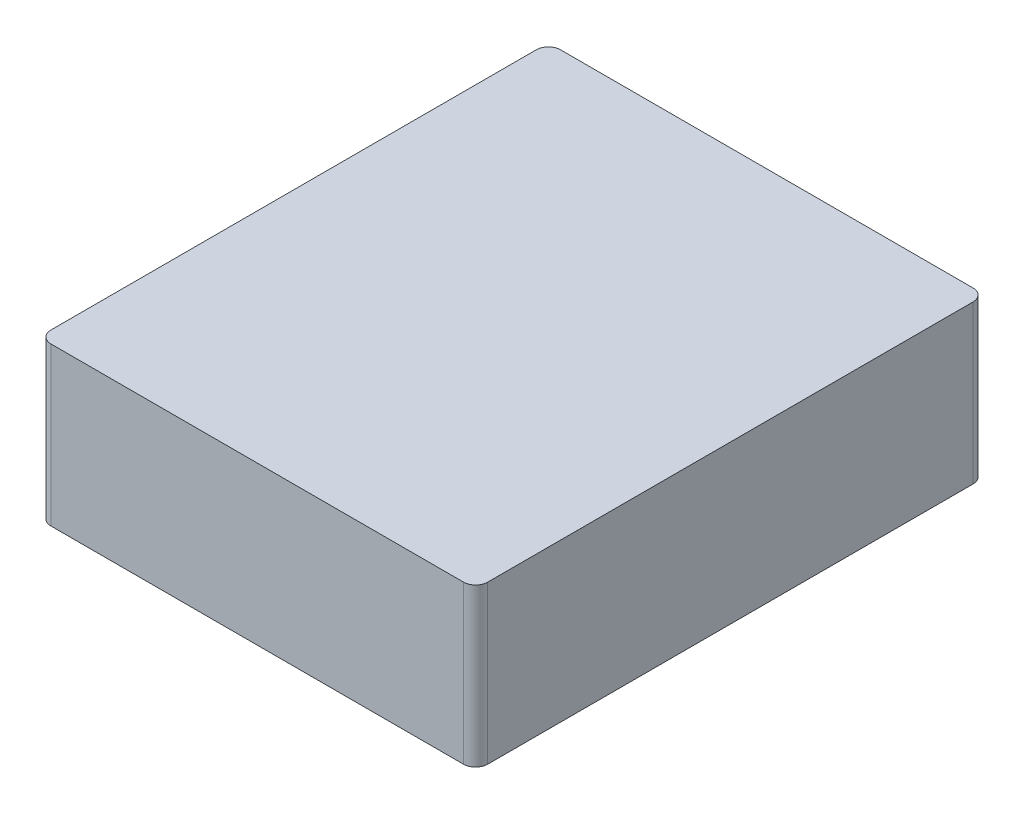
SolidWorks part; units mm, degrees
ref_plane "Front" through (0, 0, 0) normal (0, 0, 1) x (1, 0, 0)
ref_plane "Top" through (0, 0, 0) normal (0, 1, 0) x (1, 0, 0)
ref_plane "Right" through (0, 0, 0) normal (1, 0, 0) x (0, 0, -1)
sketch "Croquis1" plane through (0, 0, 0) normal (0, 1, 0) x (1, 0, 0)
  line L1 (-18, -21) -> (18, -21)
  line L2 (-18, -21) -> (-18, 21)
  line L3 (-18, 21) -> (18, 21)
  line L4 (18, -21) -> (18, 21)
  line L5 (-18, -21) -> (18, 21) construction
  line L6 (-18, 21) -> (18, -21) construction
  point P0 (0, 0)
  dimension "D1" = 42
  dimension "D2" = 36
extrude "Saliente-Extruir1" add sketch "Croquis1" along normal blind 13
fillet "Redondeo1" radius 1 4 edges at (-18, 6.5, 21) (-18, 6.5, -21) (18, 6.5, -21) (18, 6.5, 21)
